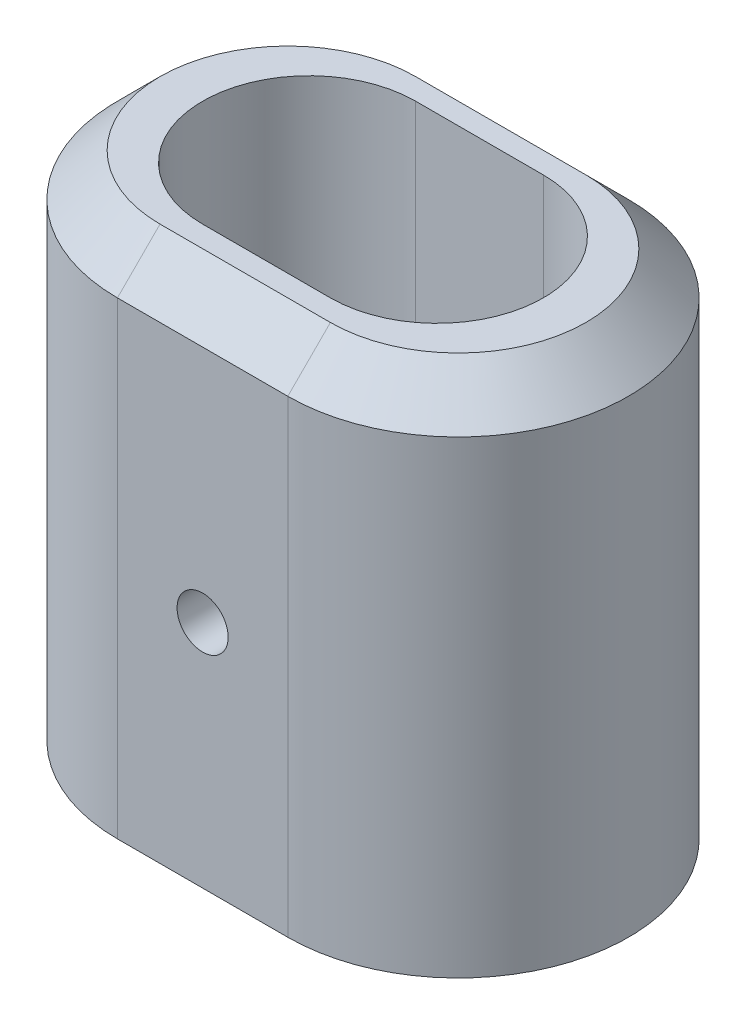
SolidWorks part; units mm, degrees
ref_plane "Alzado" through (0, 0, 0) normal (0, 0, 1) x (1, 0, 0)
ref_plane "Planta" through (0, 0, 0) normal (0, 1, 0) x (1, 0, 0)
ref_plane "Vista lateral" through (0, 0, 0) normal (1, 0, 0) x (0, 0, -1)
sketch "Croquis1" plane through (0, 0, 0) normal (0, 1, 0) x (1, 0, 0)
  line L0 (0, 0) -> (15, 0) construction
  line L1 (0, 12.5) -> (15, 12.5)
  line L2 (0, -12.5) -> (15, -12.5)
  line L3 (-12.5, 0) -> (27.5, 0) construction
  line L7 (27.5, 0) -> (37.5, 0) construction
  line L8 (-12.5, 0) -> (-22.5, 0) construction
  line L9 (-2.5, 20) -> (17.5, 20)
  line L10 (-2.5, -20) -> (17.5, -20)
  arc A0 (0, 12.5) -> (0, -12.5) centre (0, 0) ccw
  arc A1 (15, -12.5) -> (15, 12.5) centre (15, 0) ccw
  arc A5 (17.5, -20) -> (17.5, 20) centre (17.5, 0) ccw
  arc A6 (-2.5, 20) -> (-2.5, -20) centre (-2.5, 0) ccw
  point P3 (7.5, 0)
  point P11 (7.5, -12.5)
  dimension "D3" = 10
  dimension "D4" = 40
  dimension "D6" = 40
  dimension "D1" = 25
  dimension "D2" = 40
  dimension "D5" = 10
  dimension "D7" = 20
  dimension "D8" = 20
extrude "Saliente-Extruir1" add sketch "Croquis1" along normal blind 60
chamfer "Chaflán1" distance 5 angle 45 4 edges at (-22.5, 60, 0) (7.5, 60, -20) (37.5, 60, 0) (7.5, 60, 20)
sketch "Croquis2" plane through (0, 0, 20) normal (0, 0, 1) x (1, 0, 0)
  line L0 (7.5, 55) -> (7.5, 27) construction
  line L1 (17.5, 55) -> (-2.5, 55) construction
  circle A0 centre (7.5, 27) radius 3
  dimension "D2" = 6
  dimension "D1" = 28
extrude "Cortar-Extruir1" cut sketch "Croquis2" against normal blind 60
